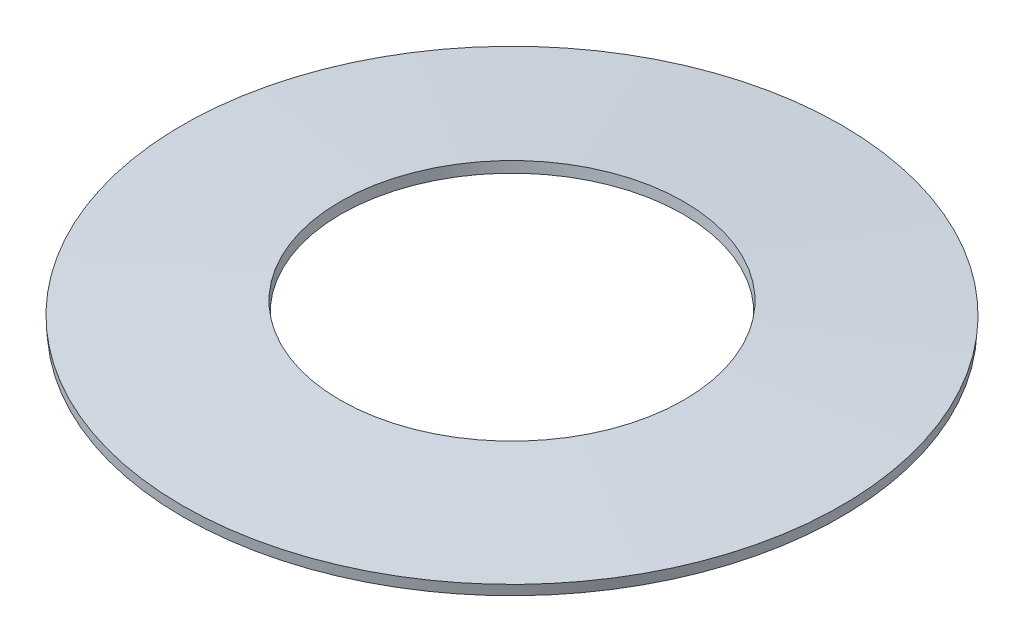
SolidWorks part; units mm, degrees
ref_plane "Front" through (0, 0, 0) normal (0, 0, 1) x (1, 0, 0)
ref_plane "Top" through (0, 0, 0) normal (0, 1, 0) x (1, 0, 0)
ref_plane "Right" through (0, 0, 0) normal (1, 0, 0) x (0, 0, -1)
sketch "Sketch1" plane through (0, 0, 0) normal (0, 0, 1) x (1, 0, 0)
  line L0 (7.8802, 0) -> (4.1, 0.3008)
  line L1 (4.1, 0.3008) -> (4.1198, 0.55)
  line L2 (4.1198, 0.55) -> (7.9, 0.2492)
  line L3 (7.9, 0.2492) -> (7.8802, 0)
  line L4 (0, 0) -> (0, 0.55) construction
  dimension "ID" = 8.2
  dimension "OD" = 15.8
  dimension "Thickness" = 0.25
  dimension "Height" = 0.55
revolve "Revolve1" add sketch "Sketch1" angle 360 about L4
